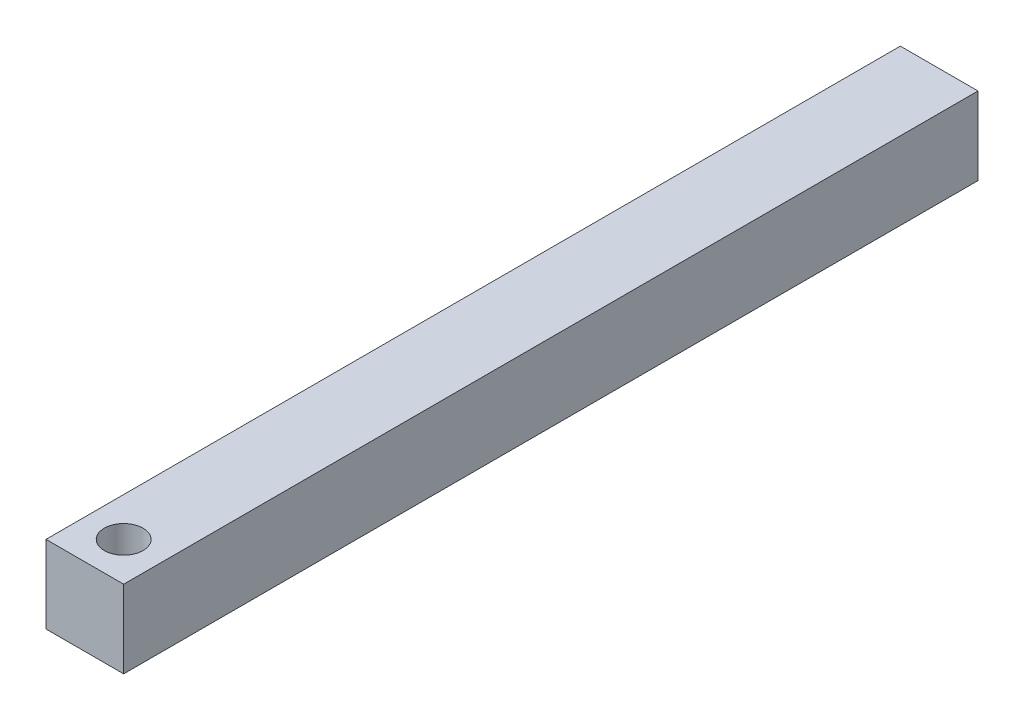
SolidWorks part; units mm, degrees
ref_plane "Front Plane" through (0, 0, 0) normal (0, 0, 1) x (1, 0, 0)
ref_plane "Top Plane" through (0, 0, 0) normal (0, 1, 0) x (1, 0, 0)
ref_plane "Right Plane" through (0, 0, 0) normal (1, 0, 0) x (0, 0, -1)
sketch "Sketch1" plane through (0, 0, 0) normal (0, 0, 1) x (1, 0, 0)
  line L1 (0, 0) -> (-25.4, 0)
  line L2 (0, 0) -> (0, 25.4)
  line L3 (0, 25.4) -> (-25.4, 25.4)
  line L4 (-25.4, 0) -> (-25.4, 25.4)
  dimension "D1" = 25.4
  dimension "D2" = 25.4
extrude "Boss-Extrude1" add sketch "Sketch1" along normal blind 279.4
sketch "Sketch2" plane through (0, 25.4, 0) normal (0, 1, 0) x (1, 0, 0)
  line L0 (0, -279.4) -> (-25.4, -279.4) construction
  line L1 (-25.4, -279.4) -> (-25.4, 0) construction
  circle A0 centre (-12.7, -266.7) radius 6.35
  point P4 (-12.7, -279.4)
  dimension "D1" = 12.7
  dimension "D2" = 12.7
extrude "Cut-Extrude1" cut sketch "Sketch2" against normal through all
